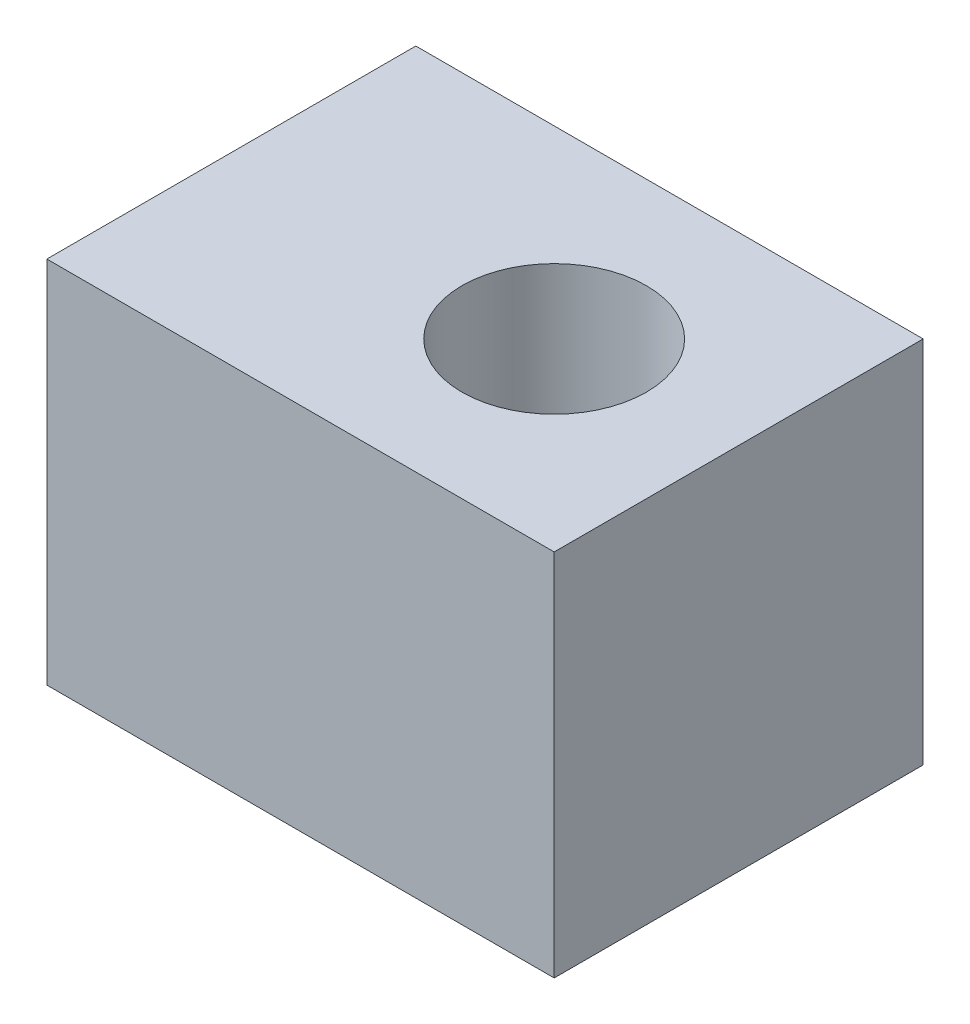
SolidWorks part; units mm, degrees
ref_plane "Front Plane" through (0, 0, 0) normal (0, 0, 1) x (1, 0, 0)
ref_plane "Top Plane" through (0, 0, 0) normal (0, 1, 0) x (1, 0, 0)
ref_plane "Right Plane" through (0, 0, 0) normal (1, 0, 0) x (0, 0, -1)
sketch "Sketch1" plane through (0, 0, 0) normal (0, 0, 1) x (1, 0, 0)
  line L0 (0, 12) -> (8, 12) construction
  line L1 (0, 0) -> (22, 0)
  line L2 (0, 0) -> (0, 16)
  line L3 (0, 16) -> (22, 16)
  line L4 (22, 0) -> (22, 16)
  line L5 (8, 12) -> (8, 4) construction
  line L6 (8, 4) -> (0, 4) construction
  line L7 (8, 8) -> (0, 8) construction
  line L8 (10, 16) -> (10, 0) construction
  line L9 (18, 16) -> (18, 0) construction
  line L10 (10, 8) -> (18, 8) construction
  line L11 (14, 8) -> (14, 0) construction
  dimension "D1" = 8
  dimension "D2" = 16
  dimension "D3" = 8
  dimension "D4" = 8
  dimension "D5" = 14
  dimension "D6" = 8
extrude "Boss-Extrude1" add sketch "Sketch1" along normal blind 16
sketch "Sketch2" plane through (0, 0, 0) normal (-1, 0, 0) x (0, 0, 1)
  line L0 (0, 16) -> (16, 0) construction
  circle A0 centre (8, 8) radius 4
  dimension "D1" = 8
extrude "Cut-Extrude1" cut sketch "Sketch2" against normal blind 8
sketch "Sketch3" plane through (0, 0, 0) normal (0, -1, 0) x (1, 0, 0)
  line L0 (14, 8) -> (22, 8) construction
  line L1 (22, 16) -> (22, 0) construction
  circle A0 centre (14, 8) radius 4
  dimension "D2" = 8
  dimension "D1" = 8
extrude "Cut-Extrude2" cut sketch "Sketch3" against normal through all
